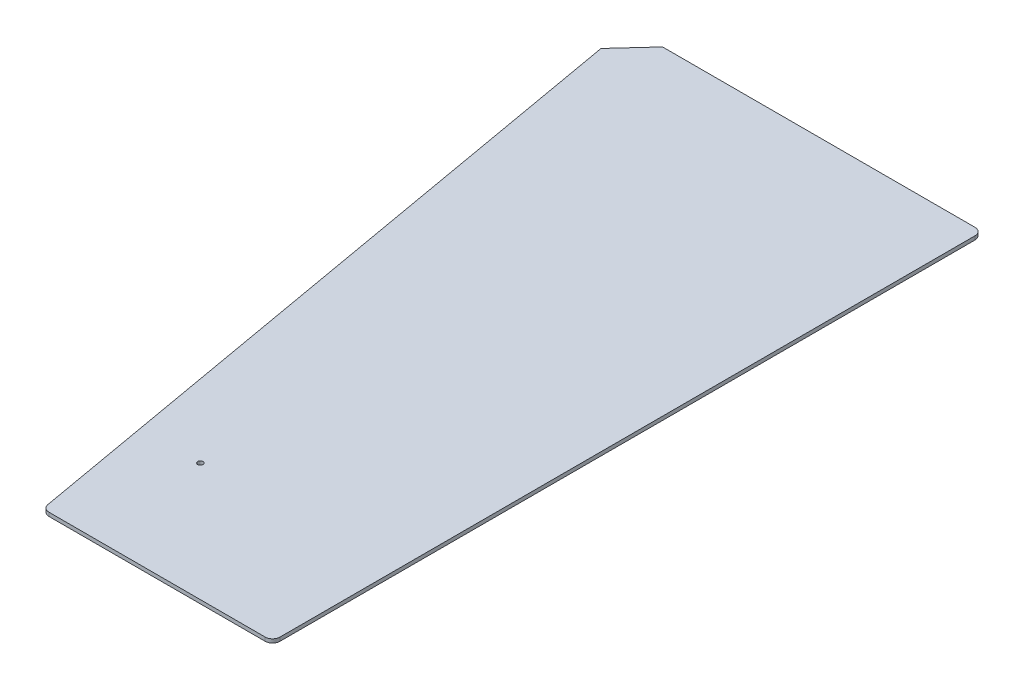
SolidWorks part; units mm, degrees
material "ABS PC"
ref_plane "Front Plane" through (0, 0, 0) normal (0, 0, 1) x (1, 0, 0)
ref_plane "Top Plane" through (0, 0, 0) normal (0, 1, 0) x (1, 0, 0)
ref_plane "Right Plane" through (0, 0, 0) normal (1, 0, 0) x (0, 0, -1)
sketch "Sketch1" plane through (0, 0, 0) normal (0, 1, 0) x (1, 0, 0)
  line L0 (-185.0249, 370.0498) -> (-154.8802, 370.0498) construction
  line L1 (-72.2077, -239.5502) -> (113.4251, -239.5502)
  line L2 (-78.4612, -234.3029) -> (-180.1603, 342.4614)
  line L3 (-154.8802, 370.0498) -> (113.4251, 370.0498)
  line L4 (119.7751, -233.2002) -> (119.7751, 363.6998)
  line L5 (-77.536, -239.5502) -> (119.7751, 370.0498) construction
  line L6 (-185.0249, 370.0498) -> (119.7751, -239.5502) construction
  line L7 (-180.1603, 342.4614) -> (-185.0249, 370.0498) construction
  line L8 (-154.8802, 370.0498) -> (-180.1603, 342.4614)
  line L9 (-185.0249, 370.0498) -> (-185.0249, -239.5502) construction
  line L10 (-185.0249, -239.5502) -> (-72.2077, -239.5502) construction
  arc A1 (119.7751, -233.2002) -> (113.4251, -239.5502) centre (113.4251, -233.2002) cw
  arc A2 (119.7751, 363.6998) -> (113.4251, 370.0498) centre (113.4251, 363.6998) ccw
  arc A4 (-72.2077, -239.5502) -> (-78.4612, -234.3029) centre (-72.2077, -233.2002) cw
  point P0 (0, 0)
  dimension "D3" = 22.225
  dimension "D5" = 6.35
  dimension "D1" = 609.6
  dimension "D2" = 304.8
  dimension "D4" = 10
  dimension "D6" = 127.5
extrude "Stock to Size" add sketch "Sketch1" along normal blind 3.175
sketch "Sketch3" [suppressed] plane through (0, 0, 0) normal (0, 0, 1) x (1, 0, 0)
  line L1 (-133.35, -361.95) -> (133.35, -361.95)
  line L2 (-139.7, -355.6) -> (-139.7, 355.6)
  line L3 (-133.35, 361.95) -> (133.35, 361.95)
  line L4 (139.7, -355.6) -> (139.7, 355.6)
  line L5 (-139.7, -361.95) -> (139.7, 361.95) construction
  line L6 (-139.7, 361.95) -> (139.7, -361.95) construction
  arc A1 (139.7, -355.6) -> (133.35, -361.95) centre (133.35, -355.6) cw
  arc A2 (139.7, 355.6) -> (133.35, 361.95) centre (133.35, 355.6) ccw
  arc A4 (-133.35, -361.95) -> (-139.7, -355.6) centre (-133.35, -355.6) cw
  arc A5 (-139.7, 355.6) -> (-133.35, 361.95) centre (-133.35, 355.6) cw
  point P0 (0, 0)
  dimension "D5" = 6.35
  dimension "D1" = 723.9
  dimension "D2" = 279.4
  dimension "D4" = 90
extrude "Front Stock" [suppressed] add sketch "Sketch3" along normal blind 3.175
sketch "Sketch2" plane through (0, 3.175, 0) normal (0, 1, 0) x (1, 0, 0)
  line L2 (-180.1603, 342.4614) -> (-78.4612, -234.3029) construction
  line L3 (-72.2077, -239.5502) -> (113.4251, -239.5502) construction
  circle A0 centre (-43.8671, -137.9502) radius 2.286
  dimension "D1" = 4.572
  dimension "D2" = 101.6
  dimension "D3" = 50.8
extrude "Mounting Hole" cut sketch "Sketch2" against normal through all
